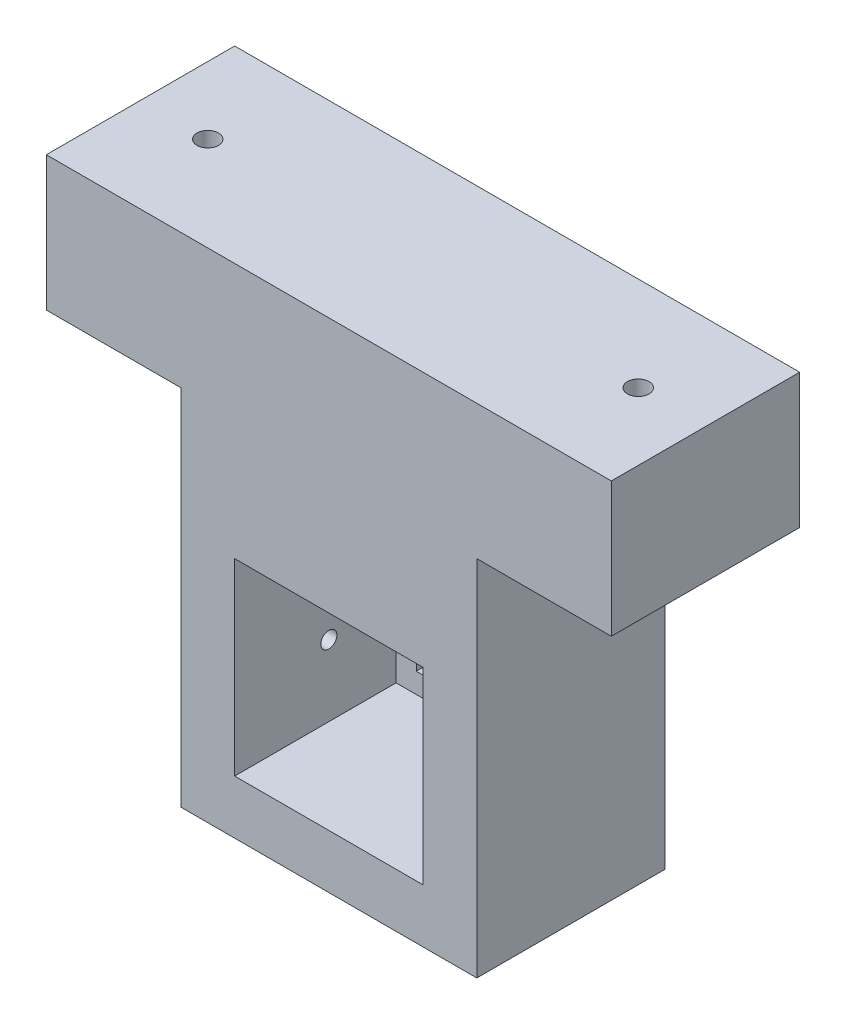
SolidWorks part; units mm, degrees
ref_plane "Plan de face" through (0, 0, 0) normal (0, 0, 1) x (1, 0, 0)
ref_plane "Plan de dessus" through (0, 0, 0) normal (0, 1, 0) x (1, 0, 0)
ref_plane "Plan de droite" through (0, 0, 0) normal (1, 0, 0) x (0, 0, -1)
sketch "Esquisse1" plane through (0, 0, 0) normal (0, 0, 1) x (1, 0, 0)
  line L1 (0, 0) -> (11, 0)
  line L2 (0, 0) -> (0, 18.5)
  line L3 (0, 18.5) -> (11, 18.5)
  line L4 (11, 0) -> (11, 18.5)
  dimension "D1" = 11
  dimension "D2" = 18.5
extrude "Boss.-Extru.1" add sketch "Esquisse1" along normal blind 7
sketch "Esquisse2" plane through (0, 0, 7) normal (0, 0, 1) x (1, 0, 0)
  line L1 (2, 9) -> (9, 9)
  line L2 (2, 9) -> (2, 2)
  line L3 (2, 2) -> (9, 2)
  line L4 (9, 9) -> (9, 2)
  line L5 (0, 0) -> (11, 0) construction
  line L6 (11, 0) -> (11, 18.5) construction
  dimension "D1" = 7
  dimension "D2" = 7
  dimension "D3" = 2
  dimension "D4" = 2
extrude "Enlèv. mat.-Extru.1" cut sketch "Esquisse2" against normal blind 6
sketch "Esquisse3" [suppressed] plane through (0, 0, 0) normal (0, 0, -1) x (-1, 0, 0)
  line L1 (-15.8125, 11.9764) -> (-7.1885, 11.9764)
  line L2 (-15.8125, 11.9764) -> (-15.8125, 6.8164)
  line L3 (-15.8125, 6.8164) -> (-7.1885, 6.8164)
  line L4 (-7.1885, 11.9764) -> (-7.1885, 6.8164)
sketch "Esquisse4" plane through (0, 0, 1) normal (0, 0, 1) x (1, 0, 0)
  line L0 (2, 2) -> (9, 2) construction
  line L1 (2.75, 8.25) -> (8.25, 8.25)
  line L2 (2.75, 8.25) -> (2.75, 2.75)
  line L3 (2.75, 2.75) -> (8.25, 2.75)
  line L4 (8.25, 8.25) -> (8.25, 2.75)
  line L5 (9, 2) -> (9, 9) construction
  dimension "D1" = 5.5
  dimension "D2" = 5.5
  dimension "D3" = 0.75
  dimension "D4" = 0.75
extrude "Enlèv. mat.-Extru.2" cut sketch "Esquisse4" against normal blind 10
sketch "Esquisse5" plane through (0, 0, 0) normal (-1, 0, 0) x (0, 0, 1)
  line L0 (7, 2) -> (7, 9) construction
  circle A0 centre (3.5, 4.64) radius 0.3
  dimension "D1" = 3.5
extrude "Enlèv. mat.-Extru.3" cut sketch "Esquisse5" against normal up to next
sketch "Esquisse7" plane through (11, 0, 0) normal (1, 0, 0) x (0, 0, -1)
  line L0 (-7, 13.5) -> (0, 13.5)
  line L1 (-7, 0) -> (-7, 18.5) construction
  line L2 (0, 0) -> (0, 18.5) construction
  line L3 (0, 13.5) -> (0, 18.5)
  line L4 (0, 18.5) -> (-7, 18.5)
  line L5 (-7, 18.5) -> (-7, 13.5)
  dimension "D1" = 5
extrude "Boss.-Extru.2" add sketch "Esquisse7" along normal blind 5
sketch "Esquisse8" plane through (0, 0, 0) normal (-1, 0, 0) x (0, 0, 1)
  line L0 (0, 13.5) -> (7, 13.5)
  line L1 (0, 18.5) -> (0, 0) construction
  line L2 (7, 18.5) -> (7, 0) construction
  line L3 (7, 18.5) -> (0, 18.5) construction
  line L4 (7, 13.5) -> (7, 18.5)
  line L5 (7, 18.5) -> (0, 18.5)
  line L6 (0, 18.5) -> (0, 13.5)
  dimension "D1" = 5
extrude "Boss.-Extru.3" add sketch "Esquisse8" along normal blind 5
sketch "Esquisse9" plane through (0, 18.5, 0) normal (0, 1, 0) x (1, 0, 0)
  line L0 (-5, -3.5) -> (-2.5, -3.5) construction
  line L1 (-5, -7) -> (-5, 0) construction
  line L3 (16, -3.5) -> (13.5, -3.5) construction
  line L4 (16, 0) -> (16, -7) construction
  circle A0 centre (-2.5, -3.5) radius 0.4
  circle A1 centre (13.5, -3.5) radius 0.4
  dimension "D2" = 2.5
  dimension "D1" = 2.5
extrude "Enlèv. mat.-Extru.4" cut sketch "Esquisse9" against normal through all
